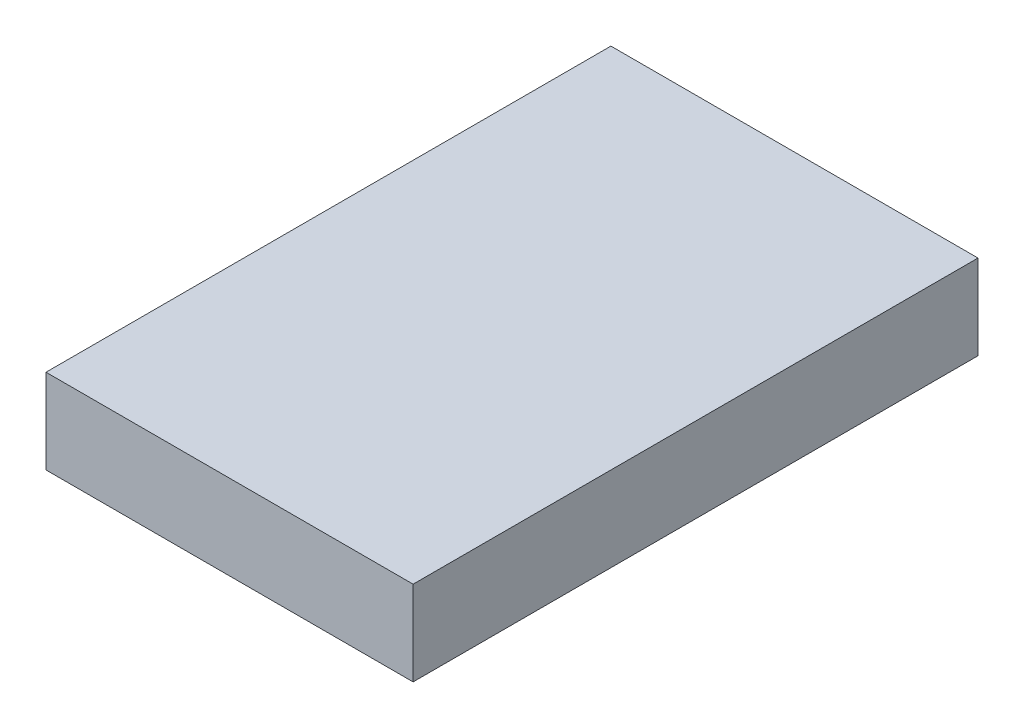
SolidWorks part; units mm, degrees
ref_plane "Ebene vorne" through (0, 0, 0) normal (0, 0, 1) x (1, 0, 0)
ref_plane "Ebene oben" through (0, 0, 0) normal (0, 1, 0) x (1, 0, 0)
ref_plane "Ebene rechts" through (0, 0, 0) normal (1, 0, 0) x (0, 0, -1)
sketch "Skizze1" plane through (0, 0, 0) normal (0, 0, 1) x (1, 0, 0)
  line L1 (207.9507, -20.0507) -> (214.4493, -20.0507)
  line L2 (207.9507, -20.0507) -> (207.9507, -21.5493)
  line L3 (207.9507, -21.5493) -> (214.4493, -21.5493)
  line L4 (214.4493, -20.0507) -> (214.4493, -21.5493)
  circle A0 centre (208.7, -20.8) radius 0.7493 construction
  circle A1 centre (213.7, -20.8) radius 0.7493 construction
extrude "Aufsatz-Linear austragen1" add sketch "Skizze1" along normal blind 10
